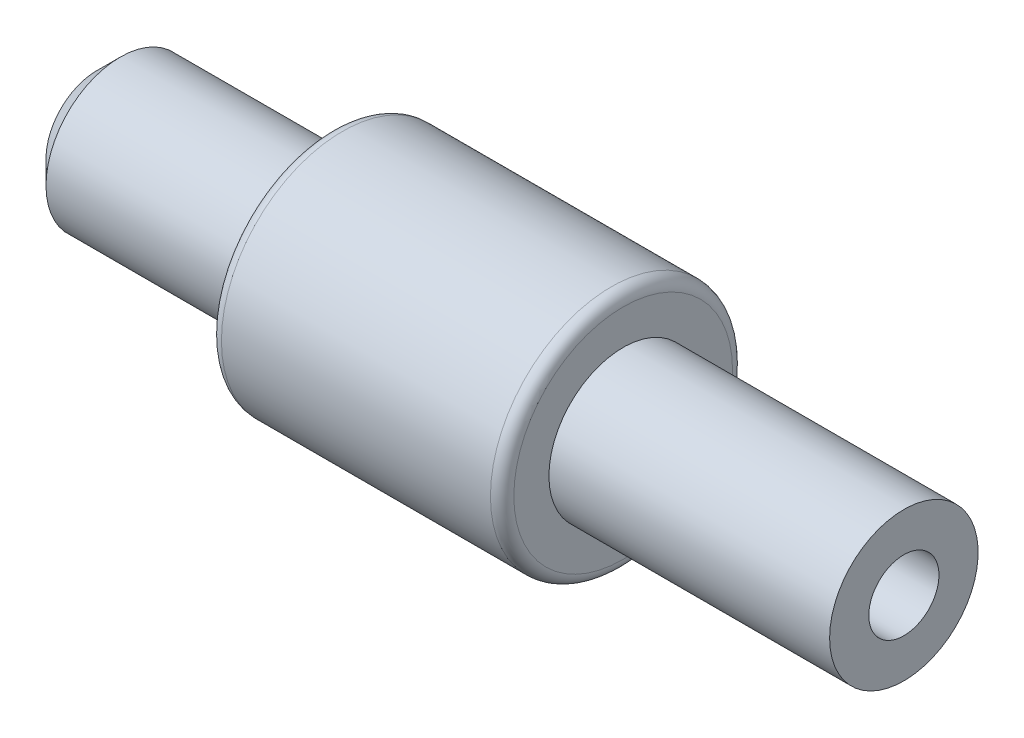
SolidWorks part; units mm, degrees
ref_plane "Front Plane" through (0, 0, 0) normal (0, 0, 1) x (1, 0, 0)
ref_plane "Top Plane" through (0, 0, 0) normal (0, 1, 0) x (1, 0, 0)
ref_plane "Right Plane" through (0, 0, 0) normal (1, 0, 0) x (0, 0, -1)
sketch "Sketch1" plane through (0, 0, 0) normal (0, 0, 1) x (1, 0, 0)
  line L0 (-42.9413, 0) -> (37.7046, 0) construction
  line L1 (24.5, 3.175) -> (12.5, 3.175)
  line L2 (12.5, 3.175) -> (12.5, 5.175)
  line L3 (12.5, 5.175) -> (0, 5.175)
  line L4 (0, 5.175) -> (0, 3.175)
  line L5 (0, 3.175) -> (-10, 3.175)
  line L6 (-10, 3.175) -> (-10, 1.5)
  line L7 (-10, 1.5) -> (24.5, 1.5)
  line L8 (24.5, 1.5) -> (24.5, 3.175)
  dimension "D1" = 3
  dimension "D2" = 10
  dimension "D3" = 12.5
  dimension "D4" = 12
  dimension "D5" = 6.35
  dimension "D6" = 2
  dimension "D7" = 6.35
revolve "Revolve1" add sketch "Sketch1" angle 360 about L0
chamfer "Chamfer1" distance 1 angle 45 1 edges at (-10, 0, 3.175)
fillet "Fillet1" radius 0.5 2 edges at (12.5, 0, 5.175) (0, 0, 5.175)
